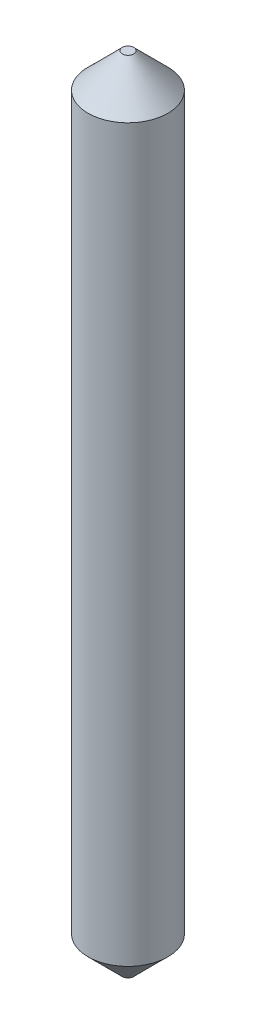
SolidWorks part; units mm, degrees
ref_plane "Спереди" through (0, 0, 0) normal (0, 0, 1) x (1, 0, 0)
ref_plane "Сверху" through (0, 0, 0) normal (0, 1, 0) x (1, 0, 0)
ref_plane "Справа" through (0, 0, 0) normal (1, 0, 0) x (0, 0, -1)
sketch "Эскиз1" plane through (0, 0, 0) normal (0, 1, 0) x (1, 0, 0)
  circle A0 centre (0, 0) radius 0.35
extrude "Бобышка-Вытянуть1" add sketch "Эскиз1" along normal blind 7
chamfer "Фаска1" distance 0.3 angle 45 2 edges at (0, 7, 0.35) (0, 0, 0.35)
